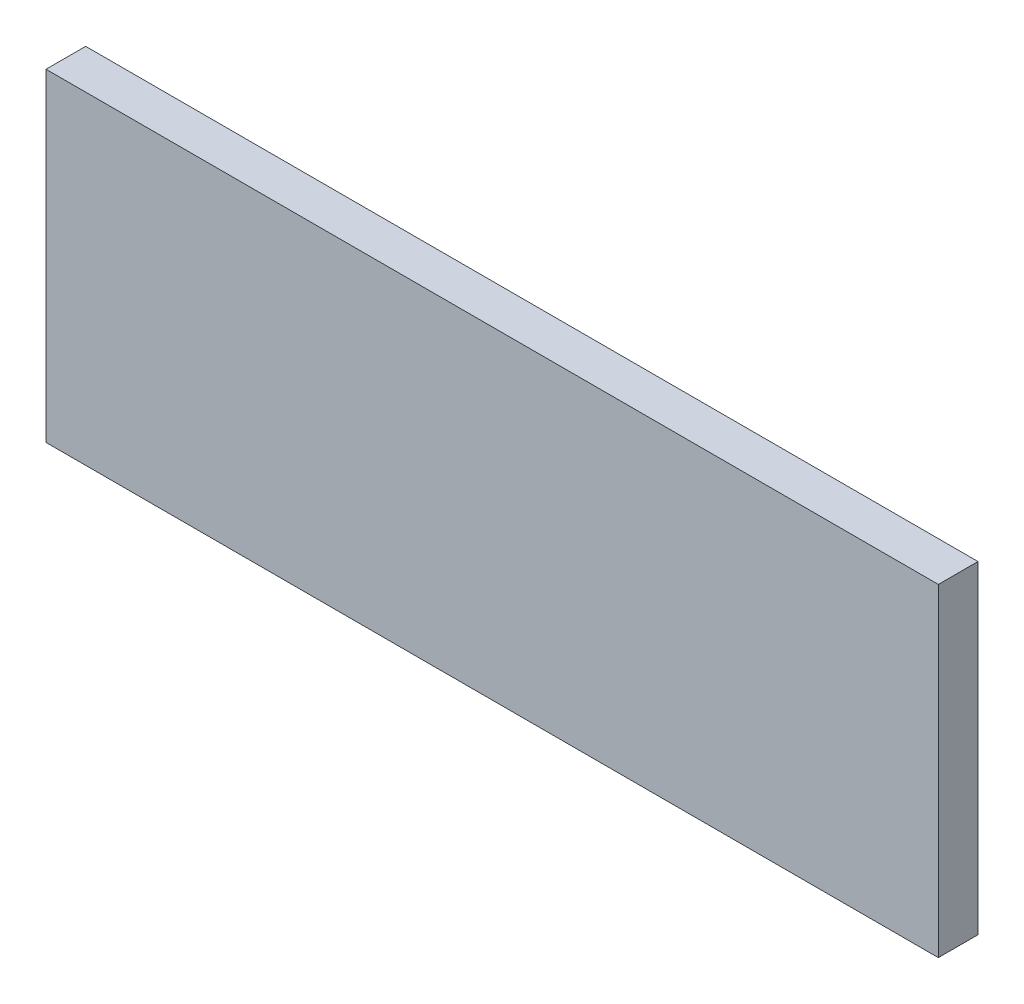
SolidWorks part; units mm, degrees
material "PUR"
ref_plane "Front Plane" through (0, 0, 0) normal (0, 0, 1) x (1, 0, 0)
ref_plane "Top Plane" through (0, 0, 0) normal (0, 1, 0) x (1, 0, 0)
ref_plane "Right Plane" through (0, 0, 0) normal (1, 0, 0) x (0, 0, -1)
sketch "Sketch1" plane through (0, 0, 0) normal (0, 0, 1) x (1, 0, 0)
  line L1 (-225, -81.5) -> (225, -81.5)
  line L2 (-225, -81.5) -> (-225, 81.5)
  line L3 (-225, 81.5) -> (225, 81.5)
  line L4 (225, -81.5) -> (225, 81.5)
  line L5 (-225, -81.5) -> (225, 81.5) construction
  line L6 (-225, 81.5) -> (225, -81.5) construction
  point P0 (0, 0)
  dimension "D1" = 450
  dimension "D2" = 163
extrude "Boss-Extrude1" add sketch "Sketch1" along normal blind 20
